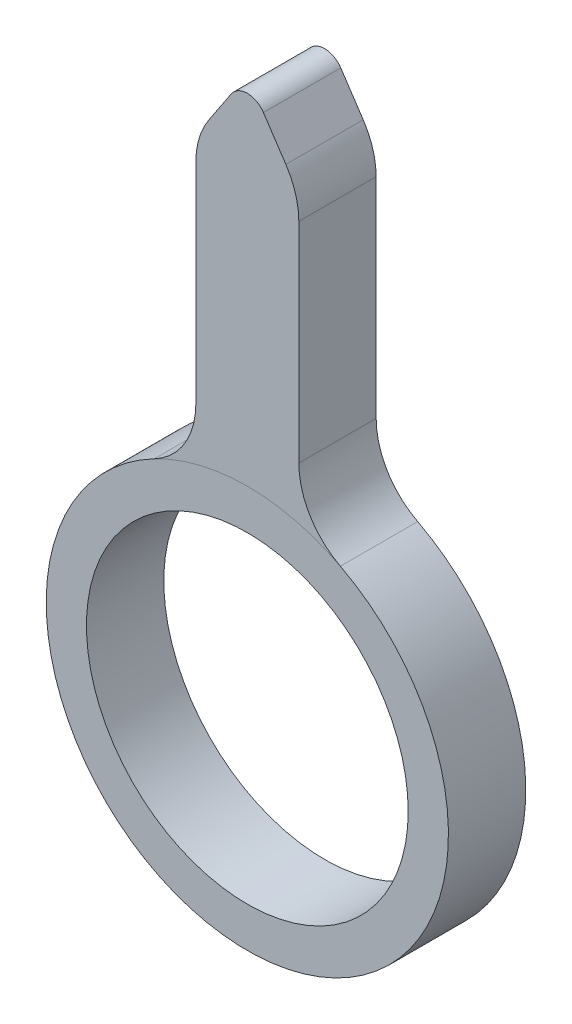
SolidWorks part; units mm, degrees
ref_plane "Front Plane" through (0, 0, 0) normal (0, 0, 1) x (1, 0, 0)
ref_plane "Top Plane" through (0, 0, 0) normal (0, 1, 0) x (1, 0, 0)
ref_plane "Right Plane" through (0, 0, 0) normal (1, 0, 0) x (0, 0, -1)
sketch "Sketch1" plane through (0, 0, 0) normal (0, 0, 1) x (1, 0, 0)
  line L0 (0, 0) -> (0, 11.43) construction
  line L1 (1.0566, 3.99) -> (1.0566, 9.8425)
  line L2 (-1.0566, 3.99) -> (-1.0566, 9.8425)
  line L3 (0, 11.43) -> (-1.0566, 9.8425)
  line L4 (0, 11.43) -> (1.0566, 9.8425)
  line L5 (-1.0566, 0) -> (-1.0566, 11.43) construction
  line L6 (1.0566, 0) -> (1.0566, 11.43) construction
  circle A0 centre (0, 0) radius 3.302
  arc A1 (-1.0566, 3.99) -> (1.0566, 3.99) centre (0, 0) ccw
  dimension "D1" = 6.604
  dimension "D3" = 8.255
  dimension "D2" = 11.43
  dimension "D4" = 1.0566
  dimension "D6" = 1.5875
  dimension "D5" = 1.0566
extrude "Boss-Extrude1" add sketch "Sketch1" along normal blind 1.5875
sketch "Sketch2" plane through (0, 0, 1.5875) normal (0, 0, 1) x (1, 0, 0)
  arc A0 (-1.0566, 3.99) -> (1.0566, 3.99) centre (0, 0) cw
split line "Split Line1"
fillet "Fillet1" radius 1.5875 2 edges at (1.0566, 9.8425, 0.7937) (-1.0566, 9.8425, 0.7937)
fillet "Fillet2" radius 0.3969 1 edges at (0, 11.43, 0.7937)
fillet "Fillet3" radius 1.5875 2 edges at (-1.0566, 3.99, 0.7937) (1.0566, 3.99, 0.7937)
